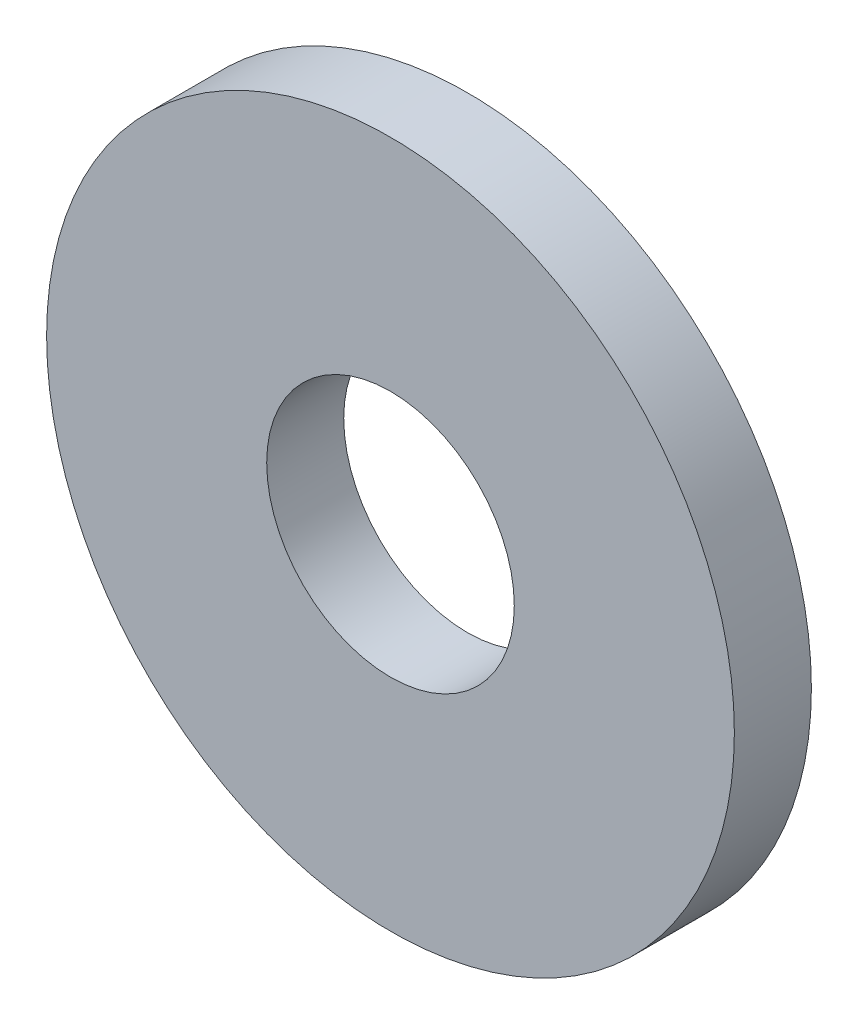
SolidWorks part; units mm, degrees
ref_plane "Front Plane" through (0, 0, 0) normal (0, 0, 1) x (1, 0, 0)
ref_plane "Top Plane" through (0, 0, 0) normal (0, 1, 0) x (1, 0, 0)
ref_plane "Right Plane" through (0, 0, 0) normal (1, 0, 0) x (0, 0, -1)
sketch "Sketch1" plane through (0, 0, 0) normal (0, 0, 1) x (1, 0, 0)
  circle A0 centre (0, 0) radius 9.525
  circle A1 centre (0, 0) radius 3.429
  dimension "D1" = 19.05
  dimension "D2" = 6.858
extrude "Boss-Extrude1" add sketch "Sketch1" along normal blind 2.1336
